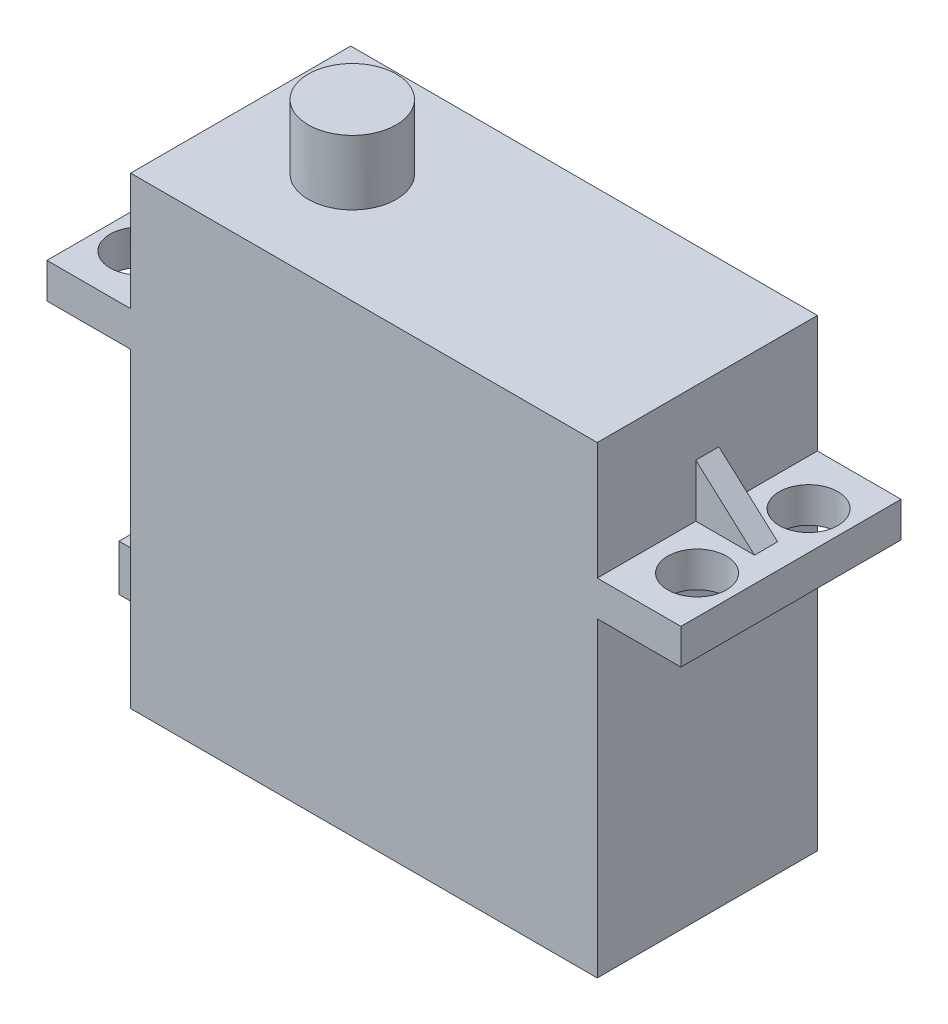
SolidWorks part; units mm, degrees
ref_plane "Front Plane" through (0, 0, 0) normal (0, 0, 1) x (1, 0, 0)
ref_plane "Top Plane" through (0, 0, 0) normal (0, 1, 0) x (1, 0, 0)
ref_plane "Right Plane" through (0, 0, 0) normal (1, 0, 0) x (0, 0, -1)
sketch "Sketch1" plane through (0, 0, 0) normal (0, 0, 1) x (1, 0, 0)
  line L1 (0, 0) -> (40.386, 0)
  line L2 (0, 0) -> (0, 40.132)
  line L3 (0, 40.132) -> (40.386, 40.132)
  line L4 (40.386, 0) -> (40.386, 40.132)
  dimension "D1" = 40.386
  dimension "D2" = 40.132
extrude "Boss-Extrude1" add sketch "Sketch1" along normal blind 19.05
sketch "Sketch2" plane through (0, 0, 19.05) normal (0, 0, 1) x (1, 0, 0)
  line L0 (0, 40.132) -> (0, 0) construction
  line L1 (0, 29.972) -> (-7.239, 29.972)
  line L2 (0, 29.972) -> (0, 26.924)
  line L3 (0, 26.924) -> (-7.239, 26.924)
  line L4 (-7.239, 29.972) -> (-7.239, 26.924)
  line L5 (40.386, 0) -> (40.386, 40.132) construction
  line L6 (40.386, 29.972) -> (47.625, 29.972)
  line L7 (40.386, 29.972) -> (40.386, 26.924)
  line L8 (40.386, 26.924) -> (47.625, 26.924)
  line L9 (47.625, 29.972) -> (47.625, 26.924)
  line L10 (0, 0) -> (40.386, 0) construction
  dimension "D1" = 26.924
  dimension "D2" = 54.864
  dimension "D3" = 3.048
extrude "Boss-Extrude2" add sketch "Sketch2" against normal up to surface (19.05 mm away) up to face at (20.193, 20.066, 0)
sketch "Sketch3" plane through (0, 29.972, 0) normal (0, 1, 0) x (1, 0, 0)
  line L3 (0, 0) -> (40.386, 0) construction
  line L4 (-3.937, -4.699) -> (44.323, -4.699) construction
  line L5 (20.193, -4.699) -> (20.193, 0) construction
  line L6 (44.323, -14.351) -> (44.323, -4.699) construction
  line L7 (47.625, 0) -> (47.625, -19.05) construction
  line L8 (47.625, -9.525) -> (44.323, -9.525) construction
  circle A0 centre (-3.937, -14.351) radius 2.54
  circle A1 centre (-3.937, -4.699) radius 2.54
  circle A2 centre (44.323, -14.351) radius 2.54
  circle A3 centre (44.323, -4.699) radius 2.54
  dimension "D1" = 5.08
  dimension "D2" = 48.26
  dimension "D4" = 9.652
extrude "Cut-Extrude1" cut sketch "Sketch3" against normal through all both and the other way through all
sketch "Sketch4" plane through (0, 40.132, 0) normal (0, 1, 0) x (1, 0, 0)
  line L0 (0, -9.525) -> (47.625, -9.525) construction
  line L1 (0, 0) -> (0, -19.05) construction
  line L2 (47.625, 0) -> (47.625, -19.05) construction
  circle A0 centre (9.66, -9.525) radius 3.81
  dimension "D1" = 7.62
  dimension "D2" = 9.66
extrude "Boss-Extrude3" add sketch "Sketch4" along normal offset from surface (5.588 mm away) 45.72 up to face at (20.193, 0, 9.525)
sketch "Sketch5" plane through (0, 0, 0) normal (-1, 0, 0) x (0, 0, 1)
  line L0 (0, 26.924) -> (0, 0) construction
  line L1 (5, 7.048) -> (14.05, 7.048)
  line L2 (5, 7.048) -> (5, 3.048)
  line L3 (5, 3.048) -> (14.05, 3.048)
  line L4 (14.05, 7.048) -> (14.05, 3.048)
  line L5 (19.05, 26.924) -> (19.05, 0) construction
  line L6 (19.05, 0) -> (0, 0) construction
  dimension "D1" = 5
  dimension "D2" = 5
  dimension "D3" = 3.048
  dimension "D4" = 4
extrude "Boss-Extrude4" add sketch "Sketch5" along normal blind 6
sketch "Sketch6" plane through (0, 0, 0) normal (0, 0, -1) x (-1, 0, 0)
  line L0 (-20.193, 40.132) -> (-20.193, 0) construction
  line L1 (-40.386, 40.132) -> (0, 40.132) construction
  line L2 (0, 0) -> (-40.386, 0) construction
  line L3 (-40.386, 17.78) -> (0, 17.78) construction
  line L4 (-40.386, 0) -> (-40.386, 26.924) construction
  line L5 (0, 26.924) -> (0, 0) construction
  circle A0 centre (-20.193, 17.78) radius 9.7122
  dimension "D1" = 17.78
ref_plane "Plane1" through (0, 0, 9.525) normal (0, 0, 1) x (1, 0, 0)
sketch "Sketch7" plane through (0, 0, 9.525) normal (0, 0, 1) x (1, 0, 0)
  line L0 (-6.35, 29.972) -> (0, 32.512)
  line L2 (0, 32.512) -> (0, 29.972)
  line L3 (0, 29.972) -> (-6.35, 29.972)
  line L4 (45.466, 29.972) -> (40.386, 34.5511)
  line L6 (40.386, 34.5511) -> (40.386, 29.972)
  line L7 (40.386, 29.972) -> (45.466, 29.972)
  line L8 (40.386, 29.972) -> (40.386, 40.132) construction
  line L9 (47.625, 29.972) -> (40.386, 29.972) construction
  line L10 (0, 29.972) -> (-7.239, 29.972) construction
  line L11 (0, 40.132) -> (0, 29.972) construction
  dimension "D1" = 6.35
  dimension "D2" = 2.54
  dimension "D3" = 5.08
extrude "Boss-Extrude5" add sketch "Sketch7" along normal mid plane 2
sketch "Sketch8" plane through (0, 0, 9.525) normal (0, 0, 1) x (1, 0, 0)
  line L0 (-604.2146, 221.5644) -> (-72.2146, 221.5644) construction
sketch "Sketch9" plane through (0, 0, 0) normal (0, 1, 0) x (1, 0, 0)
  line L0 (111.0621, 336.9998) -> (325.0621, 336.9998) construction
  line L1 (-287.2733, 54.4934) -> (-287.2733, -32.2506) construction
  circle A0 centre (8.8984, 12.2519) radius 3.3124
  dimension "D1" = 6.6247
